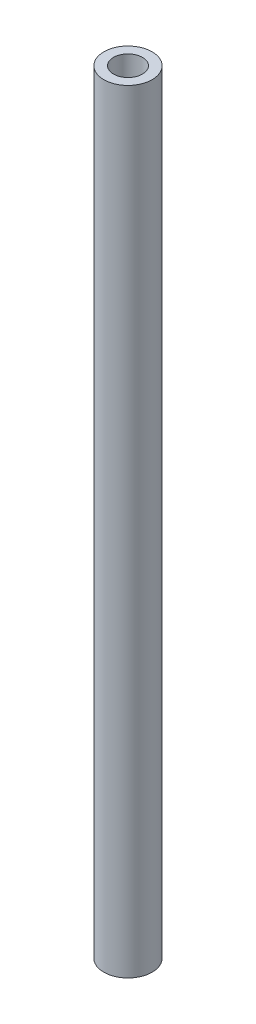
SolidWorks part; units mm, degrees
ref_plane "Front Plane" through (0, 0, 0) normal (0, 0, 1) x (1, 0, 0)
ref_plane "Top Plane" through (0, 0, 0) normal (0, 1, 0) x (1, 0, 0)
ref_plane "Right Plane" through (0, 0, 0) normal (1, 0, 0) x (0, 0, -1)
sketch "Sketch1" plane through (0, 0, 0) normal (0, 1, 0) x (1, 0, 0)
  circle A0 centre (0, 0) radius 1.5
  circle A1 centre (0, 0) radius 2.5
extrude "Boss-Extrude1" add sketch "Sketch1" along normal blind 80
